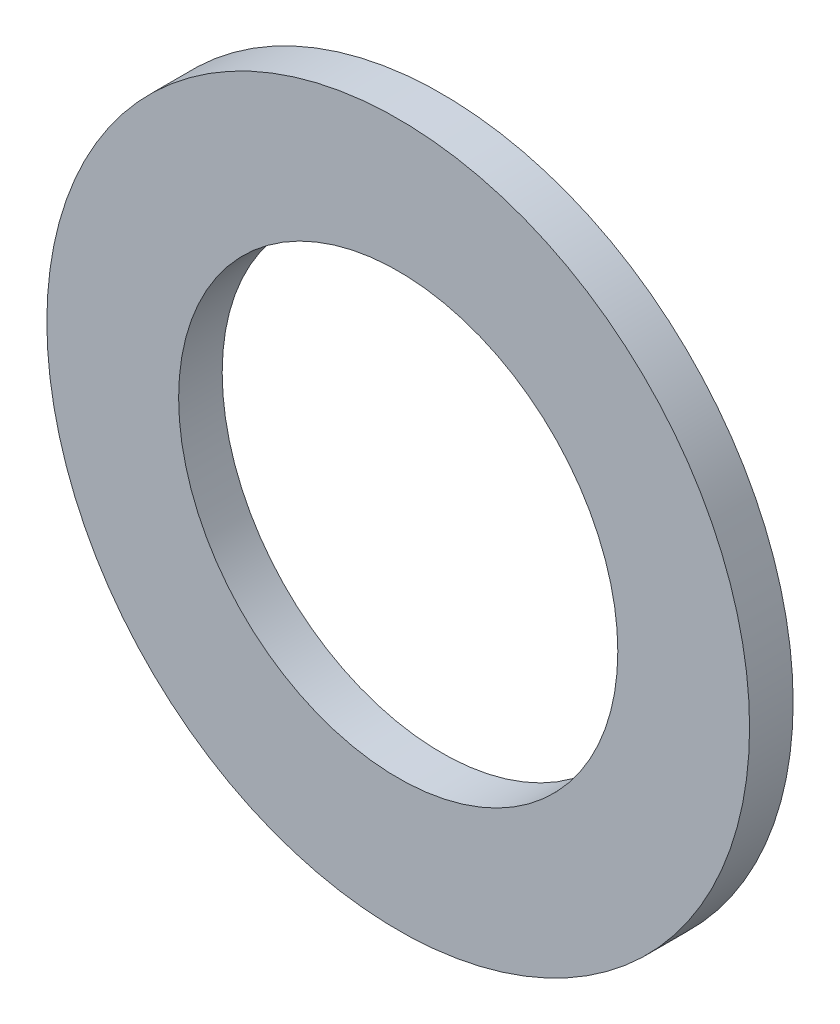
SolidWorks part; units mm, degrees
material "AISI 1020"
ref_plane "Front Plane" through (0, 0, 0) normal (0, 0, 1) x (1, 0, 0)
ref_plane "Top Plane" through (0, 0, 0) normal (0, 1, 0) x (1, 0, 0)
ref_plane "Right Plane" through (0, 0, 0) normal (1, 0, 0) x (0, 0, -1)
sketch "Sketch1" plane through (0, 0, 0) normal (0, 0, 1) x (1, 0, 0)
  circle A0 centre (0, 0) radius 7.9375
  circle A1 centre (0, 0) radius 12.7
  dimension "D1" = 15.875
  dimension "D2" = 25.4
extrude "Boss-Extrude1" add sketch "Sketch1" along normal blind 1.5748
